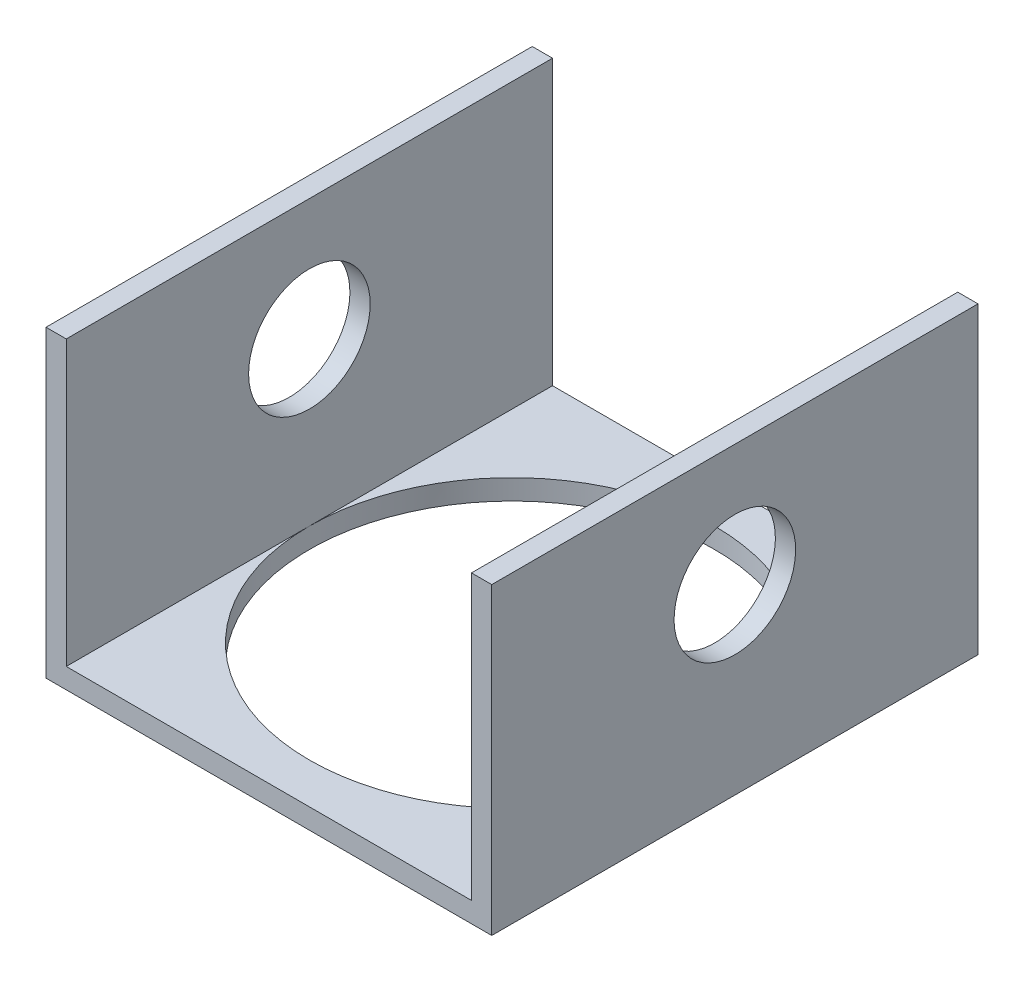
SolidWorks part; units mm, degrees
ref_plane "Front Plane" through (0, 0, 0) normal (0, 0, 1) x (1, 0, 0)
ref_plane "Top Plane" through (0, 0, 0) normal (0, 1, 0) x (1, 0, 0)
ref_plane "Right Plane" through (0, 0, 0) normal (1, 0, 0) x (0, 0, -1)
sketch "Sketch1" plane through (0, 0, 0) normal (0, 0, 1) x (1, 0, 0)
  line L0 (-31.75, 0) -> (31.75, 0)
  line L1 (31.75, 0) -> (31.75, 44.45)
  line L2 (31.75, 44.45) -> (34.925, 44.45)
  line L3 (34.925, 44.45) -> (34.925, -3.175)
  line L4 (34.925, -3.175) -> (-34.925, -3.175)
  line L5 (-34.925, -3.175) -> (-34.925, 44.45)
  line L6 (-34.925, 44.45) -> (-31.75, 44.45)
  line L7 (-31.75, 44.45) -> (-31.75, 0)
  line L8 (0, 0) -> (0, -3.175) construction
  point P4 (0, 0)
  point P11 (34.925, 25.4)
  dimension "D1" = 69.85
  dimension "D2" = 3.175
  dimension "D3" = 19.05
  dimension "D4" = 25.4
extrude "Boss-Extrude1" add sketch "Sketch1" along normal mid plane 76.2
ref_point "Point1"
sketch "Sketch2" plane through (34.925, 0, 0) normal (1, 0, 0) x (0, 0, -1)
  circle A0 centre (0, 25.4) radius 9.525
  dimension "D1" = 19.05
extrude "Cut-Extrude1" cut sketch "Sketch2" against normal through all
sketch "Sketch3" plane through (0, -3.175, 0) normal (0, -1, 0) x (1, 0, 0)
  circle A0 centre (0, 0) radius 31.75
  dimension "D1" = 63.5
extrude "Cut-Extrude2" cut sketch "Sketch3" against normal through all
